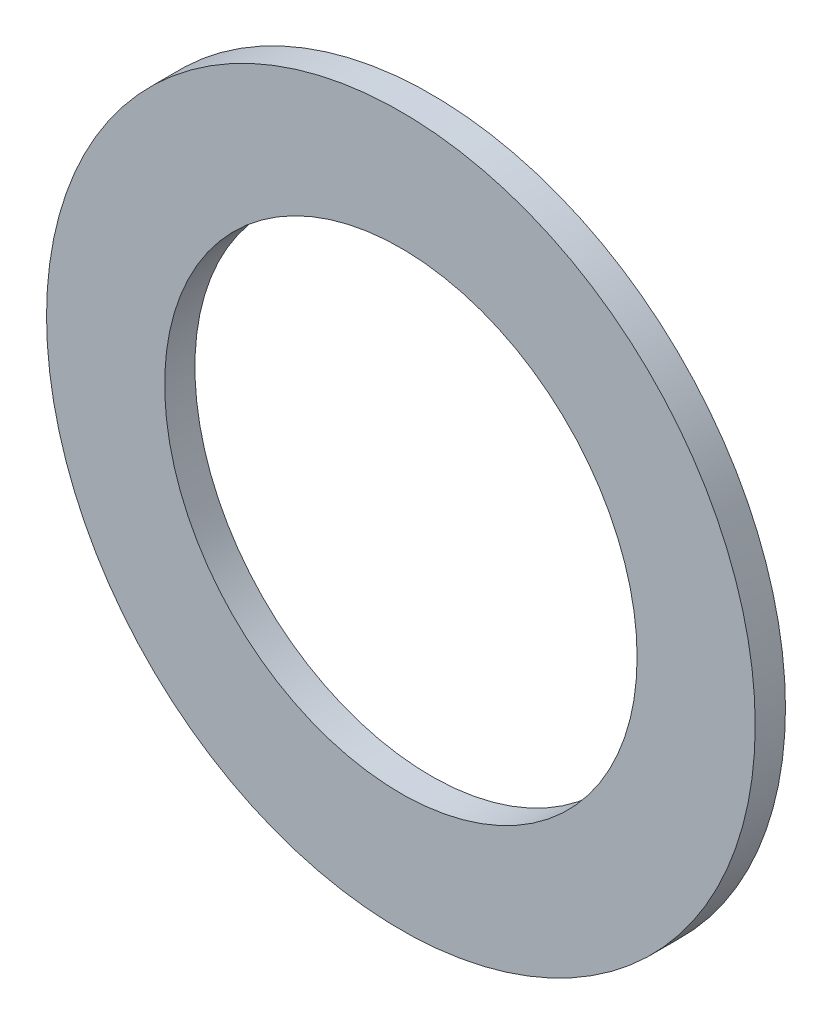
SolidWorks part; units mm, degrees
material "Plain Carbon Steel"
ref_plane "Front Plane" through (0, 0, 0) normal (0, 0, 1) x (1, 0, 0)
ref_plane "Top Plane" through (0, 0, 0) normal (0, 1, 0) x (1, 0, 0)
ref_plane "Right Plane" through (0, 0, 0) normal (1, 0, 0) x (0, 0, -1)
sketch "Sketch1" plane through (0, 0, 0) normal (0, 0, 1) x (1, 0, 0)
  circle A0 centre (0, 0) radius 6.35
  circle A1 centre (0, 0) radius 9.525
  dimension "D1" = 19.05
  dimension "D2" = 12.7
extrude "Boss-Extrude1" add sketch "Sketch1" along normal blind 0.8128
